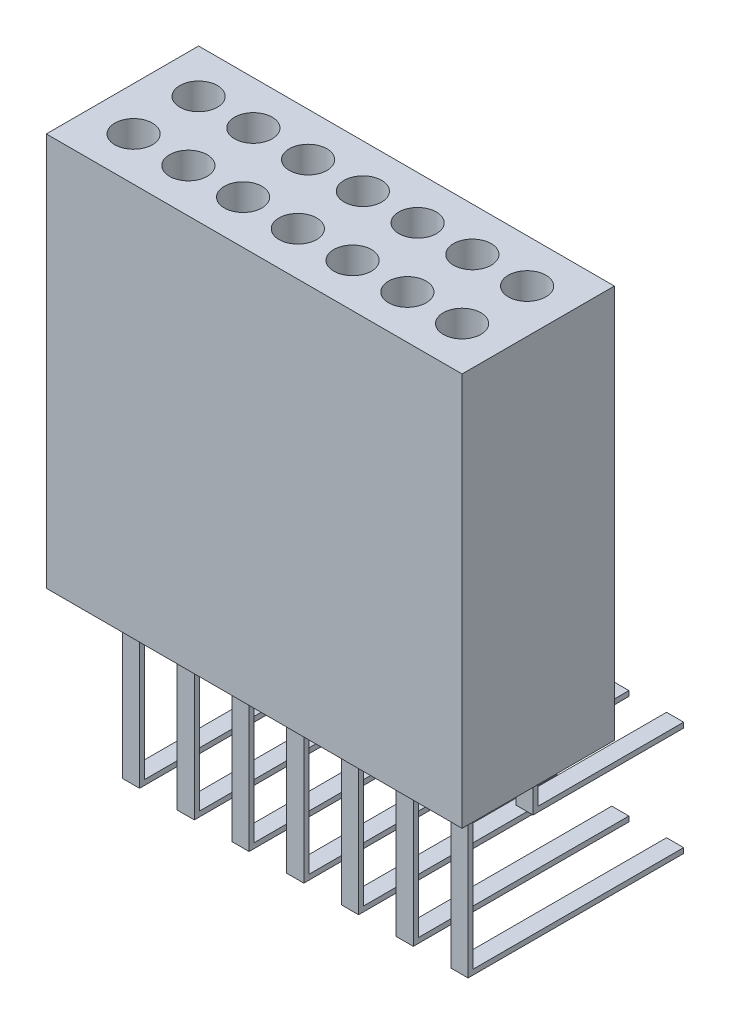
SolidWorks part; units mm, degrees
material "PEI"
ref_plane "Front Plane" through (0, 0, 0) normal (0, 0, 1) x (1, 0, 0)
ref_plane "Top Plane" through (0, 0, 0) normal (0, 1, 0) x (1, 0, 0)
ref_plane "Right Plane" through (0, 0, 0) normal (1, 0, 0) x (0, 0, -1)
sketch "Sketch2" plane through (0, 0, 0) normal (0, 1, 0) x (1, 0, 0)
  line L1 (0, 0) -> (4.86, 0)
  line L2 (0, 0) -> (0, 1.78)
  line L3 (0, 1.78) -> (4.86, 1.78)
  line L4 (4.86, 0) -> (4.86, 1.78)
  dimension "D1" = 4.86
  dimension "D2" = 1.78
extrude "Boss-Extrude1" add sketch "Sketch2" along normal blind 4.6
sketch "Sketch3" plane through (0, 4.6, 0) normal (0, 1, 0) x (1, 0, 0)
  line L0 (4.86, 1.78) -> (0, 1.78) construction
  line L1 (0, 1.78) -> (0, 0) construction
  circle A0 centre (0.51, 1.27) radius 0.22
  circle A1 centre (1.15, 1.27) radius 0.22
  circle A2 centre (1.79, 1.27) radius 0.22
  circle A3 centre (2.43, 1.27) radius 0.22
  circle A4 centre (3.07, 1.27) radius 0.22
  circle A5 centre (3.71, 1.27) radius 0.22
  circle A6 centre (4.35, 1.27) radius 0.22
  circle A7 centre (1.15, 0.51) radius 0.22
  circle A8 centre (1.79, 0.51) radius 0.22
  circle A9 centre (2.43, 0.51) radius 0.22
  circle A10 centre (3.07, 0.51) radius 0.22
  circle A11 centre (3.71, 0.51) radius 0.22
  circle A12 centre (4.35, 0.51) radius 0.22
  circle A13 centre (0.51, 0.51) radius 0.22
  dimension "D1" = 2
  dimension "D3" = 0.51
  dimension "D4" = 0.51
extrude "Cut-Extrude1" cut sketch "Sketch3" against normal blind 4.5
sketch "Sketch4" plane through (0, 0, 0) normal (0, -1, 0) x (1, 0, 0)
  line L0 (0, 0) -> (4.86, 0) construction
  line L1 (0.41, -0.48) -> (0.61, -0.48)
  line L2 (0.41, -0.48) -> (0.41, -0.54)
  line L3 (0.41, -0.54) -> (0.61, -0.54)
  line L4 (0.61, -0.48) -> (0.61, -0.54)
  line L5 (0.41, -0.48) -> (0.61, -0.54) construction
  line L6 (0.41, -0.54) -> (0.61, -0.48) construction
  line L7 (0, -1.78) -> (0, 0) construction
  line L8 (1.05, -0.48) -> (1.25, -0.48)
  line L9 (1.05, -0.48) -> (1.05, -0.54)
  line L10 (1.05, -0.54) -> (1.25, -0.54)
  line L11 (1.25, -0.48) -> (1.25, -0.54)
  line L12 (1.05, -0.48) -> (1.25, -0.54) construction
  line L13 (1.05, -0.54) -> (1.25, -0.48) construction
  line L14 (1.69, -0.48) -> (1.89, -0.48)
  line L15 (1.69, -0.48) -> (1.69, -0.54)
  line L16 (1.69, -0.54) -> (1.89, -0.54)
  line L17 (1.89, -0.48) -> (1.89, -0.54)
  line L18 (1.69, -0.48) -> (1.89, -0.54) construction
  line L19 (1.69, -0.54) -> (1.89, -0.48) construction
  line L20 (2.33, -0.48) -> (2.53, -0.48)
  line L21 (2.33, -0.48) -> (2.33, -0.54)
  line L22 (2.33, -0.54) -> (2.53, -0.54)
  line L23 (2.53, -0.48) -> (2.53, -0.54)
  line L24 (2.33, -0.48) -> (2.53, -0.54) construction
  line L25 (2.33, -0.54) -> (2.53, -0.48) construction
  line L26 (2.97, -0.48) -> (3.17, -0.48)
  line L27 (2.97, -0.48) -> (2.97, -0.54)
  line L28 (2.97, -0.54) -> (3.17, -0.54)
  line L29 (3.17, -0.48) -> (3.17, -0.54)
  line L30 (2.97, -0.48) -> (3.17, -0.54) construction
  line L31 (2.97, -0.54) -> (3.17, -0.48) construction
  line L32 (3.61, -0.48) -> (3.81, -0.48)
  line L33 (3.61, -0.48) -> (3.61, -0.54)
  line L34 (3.61, -0.54) -> (3.81, -0.54)
  line L35 (3.81, -0.48) -> (3.81, -0.54)
  line L36 (3.61, -0.48) -> (3.81, -0.54) construction
  line L37 (3.61, -0.54) -> (3.81, -0.48) construction
  line L38 (4.25, -0.48) -> (4.45, -0.48)
  line L39 (4.25, -0.48) -> (4.25, -0.54)
  line L40 (4.25, -0.54) -> (4.45, -0.54)
  line L41 (4.45, -0.48) -> (4.45, -0.54)
  line L42 (4.25, -0.48) -> (4.45, -0.54) construction
  line L43 (4.25, -0.54) -> (4.45, -0.48) construction
  point P0 (0.51, -0.51)
  point P11 (1.15, -0.51)
  point P16 (1.79, -0.51)
  point P21 (2.43, -0.51)
  point P26 (3.07, -0.51)
  point P31 (3.71, -0.51)
  point P36 (4.35, -0.51)
  dimension "D1" = 0.2
  dimension "D2" = 0.06
  dimension "D3" = 0.51
  dimension "D4" = 0.51
  dimension "D6" = 1.28
  dimension "D5" = 7
extrude "Boss-Extrude2" add sketch "Sketch4" along normal blind 1.96
sketch "Sketch6" plane through (0, 0, 0) normal (0, -1, 0) x (1, 0, 0)
  line L0 (0, -1.78) -> (0, 0) construction
  line L1 (0.41, -1.24) -> (0.61, -1.24)
  line L2 (0.41, -1.24) -> (0.41, -1.3)
  line L3 (0.41, -1.3) -> (0.61, -1.3)
  line L4 (0.61, -1.24) -> (0.61, -1.3)
  line L5 (0.41, -1.24) -> (0.61, -1.3) construction
  line L6 (0.41, -1.3) -> (0.61, -1.24) construction
  line L7 (4.86, -1.78) -> (0, -1.78) construction
  line L8 (1.05, -1.24) -> (1.25, -1.24)
  line L9 (1.05, -1.24) -> (1.05, -1.3)
  line L10 (1.05, -1.3) -> (1.25, -1.3)
  line L11 (1.25, -1.24) -> (1.25, -1.3)
  line L12 (1.05, -1.24) -> (1.25, -1.3) construction
  line L13 (1.05, -1.3) -> (1.25, -1.24) construction
  line L14 (1.69, -1.24) -> (1.89, -1.24)
  line L15 (1.69, -1.24) -> (1.69, -1.3)
  line L16 (1.69, -1.3) -> (1.89, -1.3)
  line L17 (1.89, -1.24) -> (1.89, -1.3)
  line L18 (1.69, -1.24) -> (1.89, -1.3) construction
  line L19 (1.69, -1.3) -> (1.89, -1.24) construction
  line L20 (2.33, -1.24) -> (2.53, -1.24)
  line L21 (2.33, -1.24) -> (2.33, -1.3)
  line L22 (2.33, -1.3) -> (2.53, -1.3)
  line L23 (2.53, -1.24) -> (2.53, -1.3)
  line L24 (2.33, -1.24) -> (2.53, -1.3) construction
  line L25 (2.33, -1.3) -> (2.53, -1.24) construction
  line L26 (2.97, -1.24) -> (3.17, -1.24)
  line L27 (2.97, -1.24) -> (2.97, -1.3)
  line L28 (2.97, -1.3) -> (3.17, -1.3)
  line L29 (3.17, -1.24) -> (3.17, -1.3)
  line L30 (2.97, -1.24) -> (3.17, -1.3) construction
  line L31 (2.97, -1.3) -> (3.17, -1.24) construction
  line L32 (3.61, -1.24) -> (3.81, -1.24)
  line L33 (3.61, -1.24) -> (3.61, -1.3)
  line L34 (3.61, -1.3) -> (3.81, -1.3)
  line L35 (3.81, -1.24) -> (3.81, -1.3)
  line L36 (3.61, -1.24) -> (3.81, -1.3) construction
  line L37 (3.61, -1.3) -> (3.81, -1.24) construction
  line L38 (4.25, -1.24) -> (4.45, -1.24)
  line L39 (4.25, -1.24) -> (4.25, -1.3)
  line L40 (4.25, -1.3) -> (4.45, -1.3)
  line L41 (4.45, -1.24) -> (4.45, -1.3)
  line L42 (4.25, -1.24) -> (4.45, -1.3) construction
  line L43 (4.25, -1.3) -> (4.45, -1.24) construction
  point P0 (0.51, -1.27)
  point P10 (1.15, -1.27)
  point P15 (1.79, -1.27)
  point P20 (2.43, -1.27)
  point P25 (3.07, -1.27)
  point P30 (3.71, -1.27)
  point P35 (4.35, -1.27)
  dimension "D1" = 0.2
  dimension "D2" = 0.06
  dimension "D3" = 0.51
  dimension "D4" = 0.51
  dimension "D6" = 0.64
  dimension "D5" = 7
extrude "Boss-Extrude3" add sketch "Sketch6" along normal blind 0.69
sketch "Sketch7" plane through (0, 0, -1.3) normal (0, 0, -1) x (-1, 0, 0)
  line L0 (-4.25, -0.69) -> (-4.25, 0) construction
  line L1 (-4.45, -0.69) -> (-4.25, -0.69)
  line L2 (-4.45, -0.69) -> (-4.45, -0.63)
  line L3 (-4.45, -0.63) -> (-4.25, -0.63)
  line L4 (-4.25, -0.69) -> (-4.25, -0.63)
  line L5 (-3.81, -0.69) -> (-3.61, -0.69)
  line L6 (-3.81, -0.69) -> (-3.81, -0.63)
  line L7 (-3.81, -0.63) -> (-3.61, -0.63)
  line L8 (-3.61, -0.69) -> (-3.61, -0.63)
  line L9 (-3.17, -0.69) -> (-2.97, -0.69)
  line L10 (-3.17, -0.69) -> (-3.17, -0.63)
  line L11 (-3.17, -0.63) -> (-2.97, -0.63)
  line L12 (-2.97, -0.69) -> (-2.97, -0.63)
  line L13 (-2.53, -0.69) -> (-2.33, -0.69)
  line L14 (-2.53, -0.69) -> (-2.53, -0.63)
  line L15 (-2.53, -0.63) -> (-2.33, -0.63)
  line L16 (-2.33, -0.69) -> (-2.33, -0.63)
  line L17 (-1.89, -0.69) -> (-1.69, -0.69)
  line L18 (-1.89, -0.69) -> (-1.89, -0.63)
  line L19 (-1.89, -0.63) -> (-1.69, -0.63)
  line L20 (-1.69, -0.69) -> (-1.69, -0.63)
  line L21 (-1.25, -0.69) -> (-1.05, -0.69)
  line L22 (-1.25, -0.69) -> (-1.25, -0.63)
  line L23 (-1.25, -0.63) -> (-1.05, -0.63)
  line L24 (-1.05, -0.69) -> (-1.05, -0.63)
  line L25 (-0.61, -0.69) -> (-0.41, -0.69)
  line L26 (-0.61, -0.69) -> (-0.61, -0.63)
  line L27 (-0.61, -0.63) -> (-0.41, -0.63)
  line L28 (-0.41, -0.69) -> (-0.41, -0.63)
  dimension "D1" = 0.06
extrude "Boss-Extrude4" add sketch "Sketch7" along normal blind 1.7
sketch "Sketch8" plane through (0, 0, -0.54) normal (0, 0, -1) x (-1, 0, 0)
  line L0 (-4.25, -1.96) -> (-4.45, -1.96) construction
  line L1 (-4.45, -1.96) -> (-4.25, -1.96)
  line L2 (-4.45, -1.96) -> (-4.45, -1.9)
  line L3 (-4.45, -1.9) -> (-4.25, -1.9)
  line L4 (-4.25, -1.96) -> (-4.25, -1.9)
  line L5 (-4.45, -1.96) -> (-4.45, 0) construction
  line L6 (-4.25, -1.96) -> (-4.25, 0) construction
  line L7 (-3.81, -1.96) -> (-3.61, -1.96)
  line L8 (-3.81, -1.96) -> (-3.81, -1.9)
  line L9 (-3.81, -1.9) -> (-3.61, -1.9)
  line L10 (-3.61, -1.96) -> (-3.61, -1.9)
  line L11 (-3.17, -1.96) -> (-2.97, -1.96)
  line L12 (-3.17, -1.96) -> (-3.17, -1.9)
  line L13 (-3.17, -1.9) -> (-2.97, -1.9)
  line L14 (-2.97, -1.96) -> (-2.97, -1.9)
  line L15 (-2.53, -1.96) -> (-2.33, -1.96)
  line L16 (-2.53, -1.96) -> (-2.53, -1.9)
  line L17 (-2.53, -1.9) -> (-2.33, -1.9)
  line L18 (-2.33, -1.96) -> (-2.33, -1.9)
  line L19 (-1.89, -1.96) -> (-1.69, -1.96)
  line L20 (-1.89, -1.96) -> (-1.89, -1.9)
  line L21 (-1.89, -1.9) -> (-1.69, -1.9)
  line L22 (-1.69, -1.96) -> (-1.69, -1.9)
  line L23 (-1.25, -1.96) -> (-1.05, -1.96)
  line L24 (-1.25, -1.96) -> (-1.25, -1.9)
  line L25 (-1.25, -1.9) -> (-1.05, -1.9)
  line L26 (-1.05, -1.96) -> (-1.05, -1.9)
  line L27 (-0.61, -1.96) -> (-0.41, -1.96)
  line L28 (-0.61, -1.96) -> (-0.61, -1.9)
  line L29 (-0.61, -1.9) -> (-0.41, -1.9)
  line L30 (-0.41, -1.96) -> (-0.41, -1.9)
  dimension "D1" = 0.06
extrude "Boss-Extrude5" add sketch "Sketch8" along normal blind 2.46
